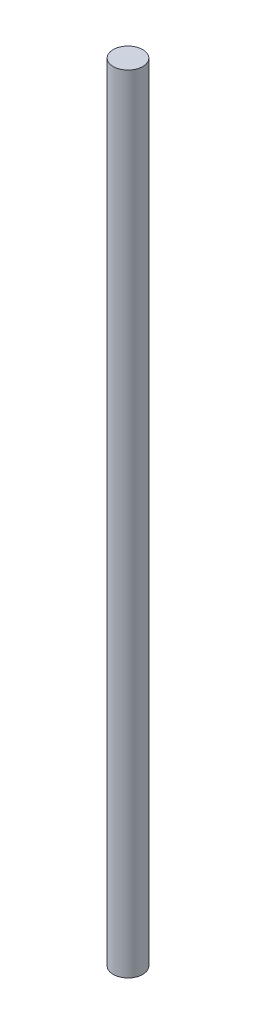
SolidWorks part; units mm, degrees
ref_plane "Front Plane" through (0, 0, 0) normal (0, 0, 1) x (1, 0, 0)
ref_plane "Top Plane" through (0, 0, 0) normal (0, 1, 0) x (1, 0, 0)
ref_plane "Right Plane" through (0, 0, 0) normal (1, 0, 0) x (0, 0, -1)
sketch "Sketch2" plane through (0, 0, 0) normal (0, 1, 0) x (1, 0, 0)
  circle A0 centre (0, 0) radius 1.5
  dimension "D1" = 3
extrude "Boss-Extrude1" add sketch "Sketch2" along normal blind 80
